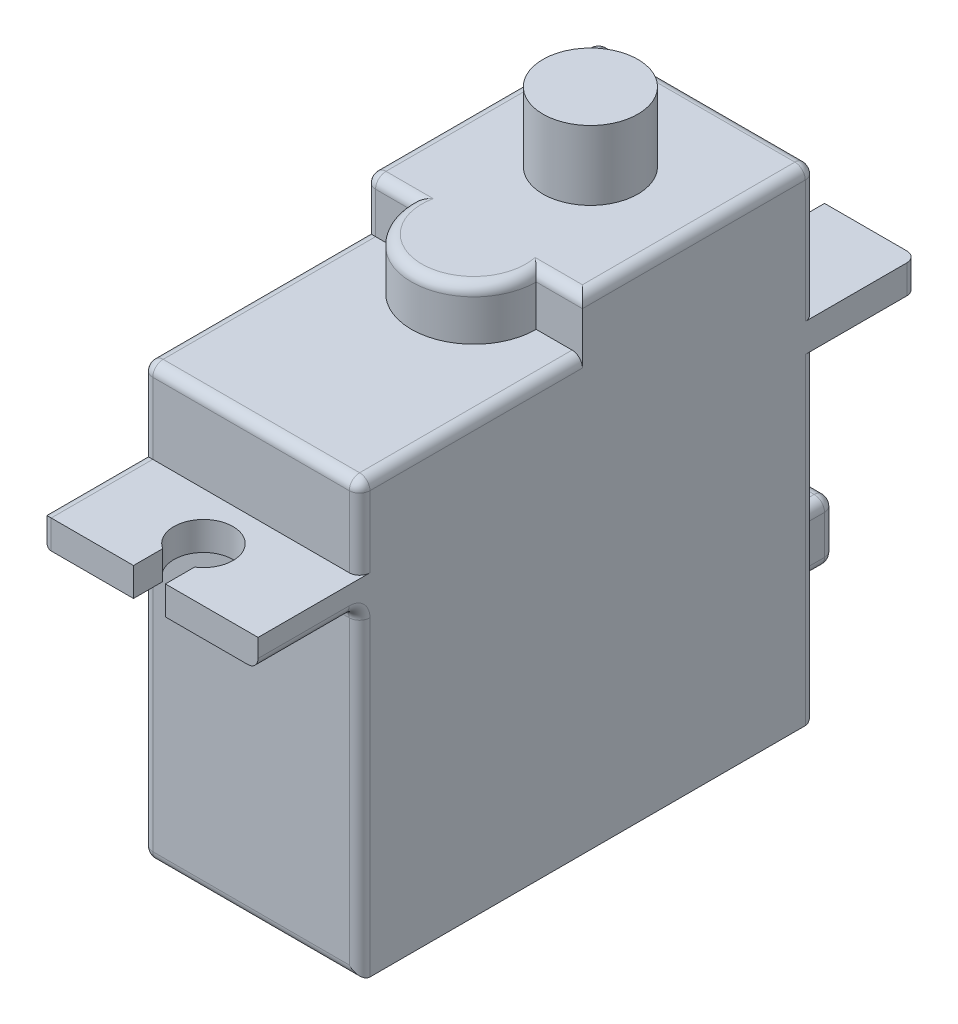
SolidWorks part; units mm, degrees
ref_plane "Front" through (0, 0, 0) normal (0, 0, 1) x (1, 0, 0)
ref_plane "Top" through (0, 0, 0) normal (0, 1, 0) x (1, 0, 0)
ref_plane "Right" through (0, 0, 0) normal (1, 0, 0) x (0, 0, -1)
sketch "Base Sketch" plane through (0, 0, 0) normal (0, 1, 0) x (1, 0, 0)
  line L1 (0, 0) -> (13.3096, 0)
  line L2 (0, 0) -> (0, 27.94)
  line L3 (0, 27.94) -> (13.3096, 27.94)
  line L4 (13.3096, 0) -> (13.3096, 27.94)
  dimension "D1" = 27.94
  dimension "D2" = 13.3096
extrude "Base" add sketch "Base Sketch" along normal blind 19.6977
sketch "Mounting Point Sketch" plane through (0, 19.6977, 0) normal (0, 1, 0) x (1, 0, 0)
  line L0 (0, 34.163) -> (0, -6.223)
  line L1 (13.3096, -6.223) -> (13.3096, 34.163)
  line L2 (13.3096, 0) -> (13.3096, 27.94) construction
  line L3 (0, 27.94) -> (0, 0) construction
  line L4 (0, -6.223) -> (0, 0) construction
  line L5 (13.3096, 0) -> (13.3096, 27.94) construction
  line L6 (0, 27.94) -> (0, 0) construction
  line L7 (0, 34.163) -> (13.3096, 34.163)
  line L8 (0, -6.223) -> (13.3096, -6.223)
  point P8 (13.3096, 13.97)
  point P12 (0, 13.97)
  dimension "D1" = 40.386
extrude "Mounting Point" add sketch "Mounting Point Sketch" along normal blind 1.7526
sketch "Mounting Holes Sketch" plane through (0, 21.4503, 0) normal (0, 1, 0) x (1, 0, 0)
  line L0 (6.6548, 32.6644) -> (6.6548, 32.3774) construction
  line L1 (13.3096, 34.163) -> (0, 34.163) construction
  line L2 (0, -6.223) -> (13.3096, -6.223) construction
  line L3 (0, 13.97) -> (13.3096, 13.97) construction
  line L4 (0, 34.163) -> (0, -6.223) construction
  line L5 (13.3096, -6.223) -> (13.3096, 34.163) construction
  line L6 (6.6548, 29.0449) -> (6.6548, -6.223) construction
  line L7 (5.6769, 34.163) -> (7.6327, 34.163)
  line L8 (5.6769, 34.163) -> (5.6769, 32.3774)
  line L10 (7.6327, 34.163) -> (7.6327, 32.3774)
  line L11 (5.6769, -6.223) -> (7.6327, -6.223)
  line L12 (5.6769, -6.223) -> (5.6769, -4.4374)
  line L13 (7.6327, -6.223) -> (7.6327, -4.4374)
  arc A0 (5.6769, 32.3774) -> (7.6327, 32.3774) centre (6.6548, 30.8546) ccw
  arc A1 (5.6769, -4.4374) -> (7.6327, -4.4374) centre (6.6548, -2.9146) cw
  point P15 (6.6548, 32.6644)
  dimension "D1" = 3.6195
  dimension "D2" = 1.7856
  dimension "D3" = 1.9558
extrude "Mounting Holes" cut sketch "Mounting Holes Sketch" against normal through all
sketch "Middle Sketch" plane through (0, 21.4503, 0) normal (0, 1, 0) x (1, 0, 0)
  line L4 (0, 0) -> (13.3096, 0)
  line L5 (13.3096, 0) -> (13.3096, 27.94)
  line L6 (13.3096, 27.94) -> (0, 27.94)
  line L7 (0, 27.94) -> (0, 0)
  line L8 (0, 0) -> (13.3096, 0)
  line L9 (13.3096, 0) -> (13.3096, 27.94)
  line L10 (5.6769, 32.3774) -> (5.6769, 34.163)
  line L11 (5.6769, 34.163) -> (0, 34.163)
  line L12 (0, 34.163) -> (0, -6.223)
  line L13 (0, -6.223) -> (5.6769, -6.223)
  line L14 (5.6769, -6.223) -> (5.6769, -4.4374)
  line L15 (7.6327, -4.4374) -> (7.6327, -6.223)
  line L16 (7.6327, -6.223) -> (13.3096, -6.223)
  line L17 (13.3096, -6.223) -> (13.3096, 34.163)
  line L18 (13.3096, 34.163) -> (7.6327, 34.163)
  line L19 (7.6327, 34.163) -> (7.6327, 32.3774)
  line L20 (5.6769, 32.3774) -> (5.6769, 34.163)
  line L21 (5.6769, 34.163) -> (0, 34.163)
  line L22 (0, 34.163) -> (0, -6.223)
  line L23 (0, -6.223) -> (5.6769, -6.223)
  line L24 (5.6769, -6.223) -> (5.6769, -4.4374)
  line L25 (7.6327, -4.4374) -> (7.6327, -6.223)
  line L26 (7.6327, -6.223) -> (13.3096, -6.223)
  line L27 (13.3096, -6.223) -> (13.3096, 34.163)
  line L28 (13.3096, 34.163) -> (7.6327, 34.163)
  line L29 (7.6327, 34.163) -> (7.6327, 32.3774)
  line L30 (13.3096, 27.94) -> (0, 27.94)
  line L31 (0, 27.94) -> (0, 0)
  arc A2 (7.6327, -4.4374) -> (5.6769, -4.4374) centre (6.6548, -2.9146) ccw
  arc A3 (5.6769, 32.3774) -> (7.6327, 32.3774) centre (6.6548, 30.8546) ccw
  arc A4 (7.6327, -4.4374) -> (5.6769, -4.4374) centre (6.6548, -2.9146) ccw
  arc A5 (5.6769, 32.3774) -> (7.6327, 32.3774) centre (6.6548, 30.8546) ccw
  line M25 (13.3096, -6.223) -> (13.3096, 34.163)
  dimension "D1" = 0
  dimension "D2" = 0
extrude "Middle" add sketch "Middle Sketch" along normal blind 4.9911 contours L30 L22 L8 M25
sketch "Top Sketch" plane through (0, 26.4414, 0) normal (0, 1, 0) x (1, 0, 0)
  line L0 (13.3096, 0) -> (13.3096, 27.94) construction
  line L1 (0, 27.94) -> (13.3096, 27.94)
  line L2 (0, 27.94) -> (0, 13.6525)
  line L3 (0, 13.6525) -> (2.8321, 13.6525)
  line L4 (13.3096, 27.94) -> (13.3096, 13.6525)
  line L5 (10.4775, 13.6525) -> (13.3096, 13.6525)
  arc A0 (2.8321, 13.6525) -> (10.4775, 13.6525) centre (6.6548, 13.6525) ccw
  dimension "D2" = 7.6454
  dimension "D1" = 14.2875
  dimension "D3" = 7.6454
  dimension "D4" = 6.6548
extrude "Top extrude" add sketch "Top Sketch" along normal blind 3.1496
sketch "Gear Sketch" plane through (0, 29.591, 0) normal (0, 1, 0) x (1, 0, 0)
  line L0 (0, 13.6525) -> (2.8321, 13.6525) construction
  line L1 (10.4775, 13.6525) -> (13.3096, 13.6525) construction
  line L2 (13.3096, 13.6525) -> (13.3096, 27.94) construction
  line L3 (0, 27.94) -> (0, 13.6525) construction
  line L4 (13.3096, 27.94) -> (0, 27.94) construction
  line L5 (0, 13.6525) -> (2.8321, 13.6525) construction
  line L6 (10.4775, 13.6525) -> (13.3096, 13.6525) construction
  line L7 (13.3096, 13.6525) -> (13.3096, 27.94) construction
  line L8 (0, 27.94) -> (0, 13.6525) construction
  line L9 (13.3096, 27.94) -> (0, 27.94) construction
  line L10 (0, 13.6525) -> (13.3096, 13.6525) construction
  line L11 (6.6548, 27.94) -> (6.6548, 13.6525) construction
  line L12 (0, 20.7963) -> (13.3096, 20.7963) construction
  circle A0 centre (6.6548, 20.7963) radius 2.9083
  dimension "D1" = 5.8166
extrude "Gear" add sketch "Gear Sketch" along normal blind 4.2418
sketch "Servo Cable Sketch" plane through (0, 0, -27.94) normal (0, 0, -1) x (-1, 0, 0)
  line L0 (-13.3096, 0) -> (0, 0) construction
  line L1 (-3.9751, 7.3914) -> (-9.3345, 7.3914)
  line L2 (-3.9751, 7.3914) -> (-3.9751, 3.7338)
  line L3 (-3.9751, 3.7338) -> (-9.3345, 3.7338)
  line L4 (-9.3345, 7.3914) -> (-9.3345, 3.7338)
  line L5 (0, 19.6977) -> (0, 0) construction
  line L6 (0, 3.7338) -> (-13.3096, 3.7338) construction
  line L7 (-13.3096, 19.6977) -> (-13.3096, 0) construction
  point P12 (-6.6548, 3.7338)
  dimension "D1" = 3.7338
  dimension "D2" = 3.9751
  dimension "D3" = 3.6576
extrude "Sevo Cable" add sketch "Servo Cable Sketch" along normal blind 5.1562
fillet "Fillet1" radius 0.635 38 edges at (13.3096, 19.6977, 3.1115) (0, 9.8488, -27.94) (0, 19.6977, -31.0515) (0, 20.574, -34.163) (0, 21.4503, -31.0515) (0, 25.5206, -27.94) (0, 29.591, -20.7963) (0, 28.0162, -13.6525) (0, 26.4414, -6.8263) (0, 23.9458, 0) (0, 21.4503, 3.1115) (0, 20.574, 6.223) (0, 19.6977, 3.1115) (0, 0, -13.97) (0, 9.8488, 0) (6.6548, 19.6977, 0) (13.3096, 9.8488, 0) (6.6548, 0, 0) (9.3345, 5.5626, -33.0962) (6.6548, 3.7338, -33.0962) (3.9751, 5.5626, -33.0962) (6.6548, 7.3914, -33.0962) (3.9751, 7.3914, -30.5181) (3.9751, 3.7338, -30.5181) (9.3345, 3.7338, -30.5181) (9.3345, 7.3914, -30.5181) (6.6548, 0, -27.94) (13.3096, 9.8488, -27.94) (13.3096, 29.591, -20.7963) (13.3096, 23.9458, 0) (6.6548, 26.4414, 0) (13.3096, 26.4414, -6.8263) (11.8935, 29.591, -13.6525) (1.4161, 29.591, -13.6525) (6.6548, 29.591, -9.8298) (6.6548, 29.591, -27.94) (13.3096, 25.5206, -27.94) (13.3096, 20.574, -34.163)
